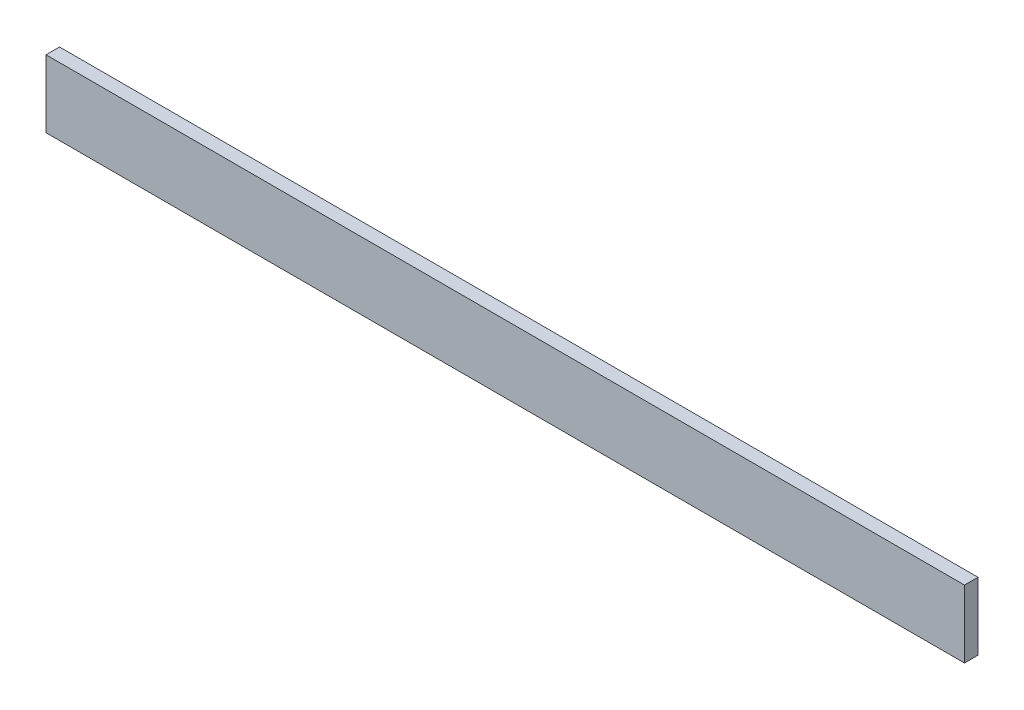
SolidWorks part; units mm, degrees
ref_plane "Спереди" through (0, 0, 0) normal (0, 0, 1) x (1, 0, 0)
ref_plane "Сверху" through (0, 0, 0) normal (0, 1, 0) x (1, 0, 0)
ref_plane "Справа" through (0, 0, 0) normal (1, 0, 0) x (0, 0, -1)
sketch "Эскиз1" plane through (0, 0, 0) normal (1, 0, 0) x (0, 0, -1)
  line L1 (0, 0) -> (10, 0)
  line L2 (0, 0) -> (0, 50)
  line L3 (0, 50) -> (10, 50)
  line L4 (10, 0) -> (10, 50)
extrude "Бобышка-Вытянуть1" add sketch "Эскиз1" along normal blind 680
